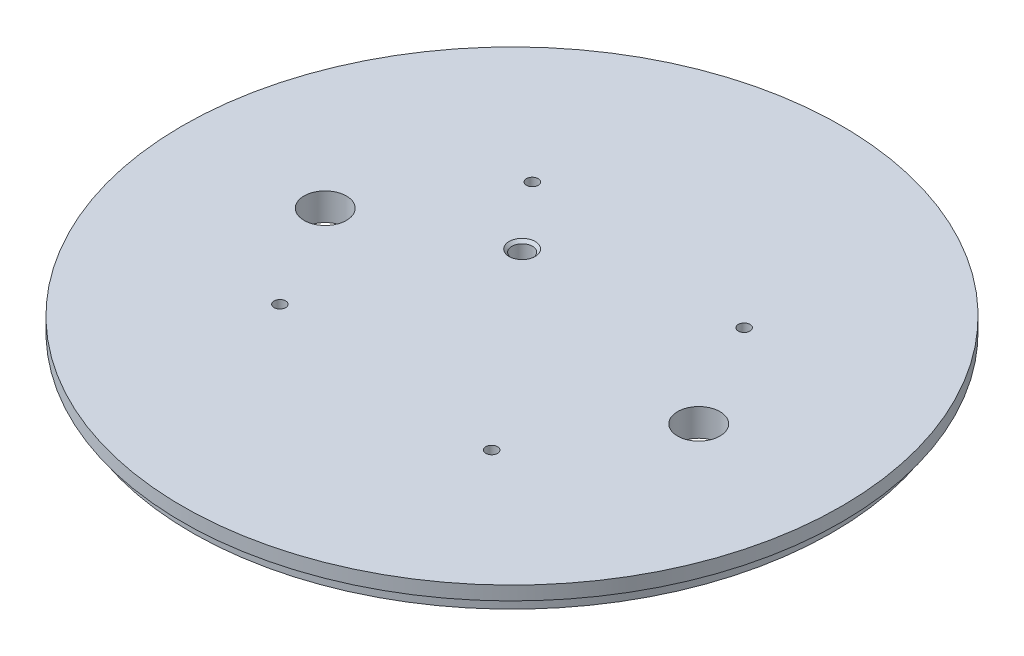
SolidWorks part; units mm, degrees
material "Delrin 2700 NC010, Low Viscosity Acetal Copolymer (SS)"
ref_plane "Front Plane" through (0, 0, 0) normal (0, 0, 1) x (1, 0, 0)
ref_plane "Top Plane" through (0, 0, 0) normal (0, 1, 0) x (1, 0, 0)
ref_plane "Right Plane" through (0, 0, 0) normal (1, 0, 0) x (0, 0, -1)
sketch "Sketch1" plane through (0, 0, 0) normal (0, 1, 0) x (1, 0, 0)
  circle A0 centre (0, 0) radius 76.2
  dimension "D1" = 152.4
extrude "Boss-Extrude1" add sketch "Sketch1" along normal blind 6.35
hole_wizard "Tap Drill for #4-40 Tap1" [suppressed] positions "Sketch3" profile "Sketch4" hole size "#4-40" standard "ANSI Inch"
sketch "Sketch3" plane through (0, 0, 0) normal (0, -1, 0) x (-1, 0, 0)
  point P0 (0, 25.4)
  point P2 (0, 50.4)
  dimension "D1" = 25.4
  dimension "D2" = 25
sketch "Sketch4" plane through (0, 0, -25.4) normal (1, 0, 0) x (0, 0, -1)
  line L0 (0, 0) -> (0, 10.16)
  line L1 (0, 10.16) -> (1.1303, 10.16)
  line L2 (1.1303, 10.16) -> (1.1303, 0)
  line L5 (1.1303, 0) -> (0, 0)
  line L11 (0, -6.35) -> (0, 107.95) construction
  dimension "Thru Hole Dia." = 2.2606
  dimension "Thru Hole Depth" = 10.16
sketch "Sketch2" [suppressed] plane through (0, 0, 0) normal (0, -1, 0) x (1, 0, 0)
  line L0 (0, 0) -> (0, -55.372) construction
  line L1 (-3.429, -27.686) -> (3.429, -27.686)
  line L2 (-5.969, -30.226) -> (-5.969, -45.574)
  line L3 (-3.429, -48.114) -> (3.429, -48.114)
  line L4 (5.969, -30.226) -> (5.969, -45.574)
  arc A0 (3.429, -48.114) -> (5.969, -45.574) centre (3.429, -45.574) ccw
  arc A1 (-5.969, -45.574) -> (-3.429, -48.114) centre (-3.429, -45.574) ccw
  arc A2 (3.429, -27.686) -> (5.969, -30.226) centre (3.429, -30.226) cw
  arc A3 (-3.429, -27.686) -> (-5.969, -30.226) centre (-3.429, -30.226) ccw
  circle A4 centre (0, -25.4) radius 1.1303 construction
  circle A5 centre (0, -50.4) radius 1.1303 construction
  point P10 (5.969, -27.686)
  point P13 (-5.969, -27.686)
  point P17 (0, -27.686)
  dimension "D2" = 2.54
  dimension "D1" = 11.938
  dimension "D3" = 2.286
  dimension "D4" = 2.286
extrude "Cut-Extrude1" [suppressed] cut sketch "Sketch2" against normal through all
hole_wizard "Tap Drill for #6-32 Tap1" positions "Sketch5" profile "Sketch6" hole size "#6-32" standard "ANSI Inch" end condition through all
sketch "Sketch5" plane through (0, 0, 0) normal (0, -1, 0) x (-1, 0, 0)
  line L0 (0, 0) -> (58.3519, 0) construction
  line L2 (0, 0) -> (37.5212, 6.616) construction
  point P0 (37.5212, 6.616)
  dimension "D1" = 10
  dimension "D2" = 38.1
sketch "Sketch6" plane through (-37.5212, 0, -6.616) normal (1, 0, 0) x (0, 0, -1)
  line L0 (0, 0) -> (0, 6.35)
  line L1 (0, 6.35) -> (1.3525, 6.35)
  line L2 (1.3525, 6.35) -> (1.3525, 0)
  line L5 (1.3525, 0) -> (0, 0)
  line L11 (0, -6.35) -> (0, 107.95) construction
  dimension "Thru Hole Dia." = 2.7051
  dimension "Thru Hole Depth" = 6.35
pattern_circular "CirPattern1" count 4 over 360 about axis through (0, 0, 0) along (0, 1, 0) of "Tap Drill for #6-32 Tap1"
hole_wizard "W (0.386) Diameter Hole1" positions "Sketch7" profile "Sketch8" hole size "W" standard "ANSI Inch" end condition through all
sketch "Sketch7" plane through (0, 0, 0) normal (0, -1, 0) x (-1, 0, 0)
  line L2 (0, 0) -> (-33.0778, 27.7556) construction
  line L4 (0, 0) -> (0, 19.4817) construction
  point P0 (-33.0778, 27.7556)
  point P17 (33.0778, -27.7556)
  dimension "D1" = 50
  dimension "D2" = 43.18
  dimension "D3" = 43.18
sketch "Sketch8" plane through (33.0778, 0, -27.7556) normal (1, 0, 0) x (0, 0, -1)
  line L0 (0, 0) -> (0, 6.35)
  line L1 (0, 6.35) -> (4.9022, 6.35)
  line L2 (4.9022, 6.35) -> (4.9022, 0)
  line L5 (4.9022, 0) -> (0, 0)
  line L11 (0, -6.35) -> (0, 107.95) construction
  dimension "Thru Hole Dia." = 9.8044
  dimension "Thru Hole Depth" = 6.35
hole_wizard "3/16 (0.1875) Diameter Hole1" positions "Sketch10" profile "Sketch11" hole size "3/16" standard "ANSI Inch" end condition through all
sketch "Sketch10" plane through (0, 0, 0) normal (0, -1, 0) x (-1, 0, 0)
  line L0 (0, 0) -> (37.5212, 6.616) construction
  point P0 (18.7606, 3.308)
sketch "Sketch11" plane through (-18.7606, 0, -3.308) normal (1, 0, 0) x (0, 0, -1)
  line L0 (0, 0) -> (0, 6.35)
  line L1 (0, 6.35) -> (3.0162, 6.35)
  line L2 (2.3812, 5.715) -> (2.3812, 0.635)
  line L3 (2.3812, 0.635) -> (3.0162, 0)
  line L5 (3.0162, 0) -> (0, 0)
  line L6 (-2.3812, 0.635) -> (-3.0162, 0) construction
  line L7 (3.0162, 6.35) -> (2.3812, 5.715)
  line L8 (-3.0162, 6.35) -> (-2.3812, 5.715) construction
  line L11 (0, -6.35) -> (0, 107.95) construction
  dimension "Thru Hole Dia." = 4.7625
  dimension "Thru Hole Depth" = 6.35
  dimension "Near C'Sink Dia." = 6.0325
  dimension "Near C'Sink Angle" = 90
  dimension "Far C'Sink Dia." = 6.0325
  dimension "Far C'Sink Angle" = 90
sketch "Sketch12" plane through (0, 0, 0) normal (0, -1, 0) x (1, 0, 0)
  line L0 (0, 0) -> (31.6547, 37.7246) construction
  line L10 (19.8869, 28.7385) -> (24.8486, 24.5751)
  line L11 (19.8869, 28.7385) -> (6.4989, 12.7833)
  line L12 (6.4989, 12.7833) -> (11.4606, 8.62)
  line L13 (24.8486, 24.5751) -> (11.4606, 8.62)
  line L17 (0, 0) -> (-53.1972, 0) construction
  line L18 (-33.0778, 27.7556) -> (33.0778, -27.7556) construction
  circle A0 centre (22.3677, 26.6568) radius 3.2385
  circle A1 centre (8.9797, 10.7016) radius 3.2385
  circle A2 centre (33.0778, -27.7556) radius 4.9022 construction
  circle A3 centre (-33.0778, 27.7556) radius 4.9022 construction
  circle A4 centre (33.0778, -27.7556) radius 4.9022
  circle A5 centre (-33.0778, 27.7556) radius 4.9022
  dimension "D1" = 6.477
  dimension "D2" = 13.97
  dimension "D3" = 20.828
extrude "Cut-Extrude4" cut sketch "Sketch12" against normal blind 3.175 contours A1 L13 A0 L11 | L10 A0 | L12 A1 | L12 A1 | L10 A0
ref_plane "Plane1" through (0, 0, 0) normal (0.6428, 0, 0.766) x (0.766, 0, -0.6428)
mirror "Mirror1" about plane through (0, 0, 0) normal (0.6428, 0, 0.766) of "Cut-Extrude4"
sketch "Sketch15" plane through (0, 0, 0) normal (0, -1, 0) x (1, 0, 0)
  circle A0 centre (0, 0) radius 74.041
  circle A1 centre (0, 0) radius 76.2 construction
  circle A2 centre (0, 0) radius 76.2
  dimension "D1" = 148.082
extrude "Cut-Extrude5" cut sketch "Sketch15" against normal blind 3.175
sketch "Sketch17" plane through (0, 6.35, 0) normal (0, 1, 0) x (1, 0, 0)
  circle A0 centre (-33.0778, -27.7556) radius 9.525
  circle A1 centre (33.0778, 27.7556) radius 9.525
  dimension "D1" = 19.05
  dimension "D2" = 19.05
split line "Split Line1" [suppressed]
sketch "Sketch19" plane through (0, 0, 0) normal (0, -1, 0) x (1, 0, 0)
  circle A0 centre (-33.0778, 27.7556) radius 9.525
  circle A1 centre (33.0778, -27.7556) radius 9.525
  dimension "D1" = 19.05
  dimension "D2" = 19.05
split line "Split Line2" [suppressed]
sketch "Sketch18" [suppressed] plane through (0, 6.35, 0) normal (0, 1, 0) x (1, 0, 0)
  circle A0 centre (0, 0) radius 76.2 construction
  circle A1 centre (33.0778, 27.7556) radius 9.525 construction
  circle A2 centre (-33.0778, -27.7556) radius 9.525 construction
  circle A3 centre (0, 0) radius 76.2
  circle A4 centre (33.0778, 27.7556) radius 9.525
  circle A5 centre (-33.0778, -27.7556) radius 9.525
  circle A7 centre (0, 0) radius 12.7
  circle A8 centre (-18.7606, 3.308) radius 9.525
  dimension "D1" = 25.4
  dimension "D2" = 19.05
extrude "Cut-Extrude6" [suppressed] cut sketch "Sketch18" against normal blind 4.7625
sketch "Sketch20" [suppressed] plane through (0, 6.35, 0) normal (0, 1, 0) x (1, 0, 0)
  line L0 (-5.3508, -4.4899) -> (5.3508, 4.4899) construction
  line L1 (5.7551, 2.6836) -> (64.7444, 30.1908)
  line L2 (0, 0) -> (-82.2548, -38.356) construction
  line L3 (0, 0) -> (46.1621, 65.9264) construction
  line L4 (0, 0) -> (-109.7287, 0) construction
  line L5 (3.6422, 5.2016) -> (40.9749, 58.5182)
  line L6 (-64.7444, -30.1908) -> (-5.7551, -2.6836)
  line L7 (-40.9749, -58.5182) -> (-3.6422, -5.2016)
  circle A0 centre (0, 0) radius 71.4375
  circle A1 centre (0, 0) radius 6.35
  circle A2 centre (-62.2864, -23.7898) radius 4.7625
  circle A4 centre (34.2443, 57.2091) radius 4.7625
  circle A7 centre (1.8576, 10.9561) radius 4.7625
  circle A8 centre (-11.1123, 0.0731) radius 4.7625
  circle A9 centre (-1.8576, -10.9561) radius 4.7625
  circle A10 centre (11.1123, -0.0731) radius 4.7625
  circle A11 centre (62.2864, 23.7898) radius 4.7625
  circle A12 centre (-34.2443, -57.2091) radius 4.7625
  dimension "D1" = 142.875
  dimension "D2" = 12.7
  dimension "D4" = 9.525
  dimension "D3" = 25
  dimension "D5" = 150
extrude "Cut-Extrude7" [suppressed] cut sketch "Sketch20" against normal blind 2.54
move or copy body "Body-Move/Copy1" bodies to move or copy 111 copy no rotation origin (0, 0, 0) rotation axis (0, -1, 0) rotation angle 40
chamfer "Chamfer1" [suppressed] distance 0.635 angle 45
equation "\"Bodytube_OD\" = 6.17in"
equation "\"Bodytube_ID\" = 5.998in"
equation "\"Camera_Cutout_Width\"=10mm"
equation "\"Camera_Cutout_Height\"=7mm"
equation "\"Fwd_Tube_Length\" = 38.5in"
equation "\"BKHD_Screw_Diam\"= 3.5mm"
equation "\"Fwd_BKHD_From_Top\" = 18in"
equation "\"Shear_Screw_Diameter\" = 0.086in"
equation "\"Shear_Screw_Coupler_Location\" = 4.5in"
equation "\"Motor_OD\" = 4in"
equation "\"Mid_Coupler_Length\" = 13in"
equation "\"Aft_Section_Length\"= 36in"
equation "\"AB_Coupler_OD_Length\"= 1in"
equation "\"AB_Coupling_Section_Length\"= 0.375in"
equation "\"AB_Coupler_Length\"= \"AB_Coupler_OD_Length\" + \"AB_Coupling_Section_Length\" * 2"
equation "\"Cutout_Angle\" = 80"
equation "\"AB_Paddle_Height\" = 0.375in"
equation "\"AB_Coupler_Num_Screws\"= 4"
equation "\"AB_BKHD_Thickness\" = 0.375in"
equation "\"AB_Mount_From_Bottom\" = 23.175in"
equation "\"Num_Cutouts\" = 3"
equation "\"AB_Coupler_OD\"= 6.17in"
equation "\"AB_Coupler_ID\"= 5.75in"
equation "\"AB_Coupler_Surface_Diameter\"= 5.998in"
equation "\"AB_Coupling_Screw_Diameter\"= 0.15748in"
equation "\"AB_Central_Bushing_Length\" = .4724in"
equation "\"Lead_Screw_Dist\" = 3.4in"
equation "\"Lead_Screw_Diam\" = 0.386in"
equation "\"Lead_Screw_Length\" = (\"Mid_Coupler_Length\" + 2*0.375in + 2*.75in)"
equation "\"Paddle_Pin_Offset\" = .25in"
equation "\"Paddle_Pin_Radius\" = 2.25in"
equation "\"SS_Paddle_Pin_Radius\" = 2.25*0.66in"
equation "\"Paddle_Gear_OD\" = 3.2in"
equation "\"Drive_Gear_OD\" = 1.7in"
equation "\"Fin_Thickness\"= .118in"
equation "\"Guiderail_Cutout_Diameter\"= 1.5in"
equation "\"DB9_Hole_Dist\" = 25mm"
equation "\"DB9_Relief_Width\" = 0.47in"
equation "\"DB9_Relief_Hole_Offset\" = 0.09in"
equation "\"Airbrakes_Wire_Hole_Dia\" = .25in"
equation "\"Airbrakes_Wire_Hole_Dist\" = 1.1in"
equation "\"Servo_Gear_Offset\" = 0.5in"
equation "\"FWD_Shear_Screw_Dist\" = 1.5in"
equation "\"Camera_Screw_Dia\" = 0.216535"
equation "\"Camera_Hole_Angle\" = atn ( 2 / 3 * tan ( 12.5deg ) )"
equation "\"Coupler_OD\" = 5.998"
equation "\"Coupler_ID\" = 5.8"
equation "\"Mounting_Bracket_Centerhole_DIA\" = 0.4in"
equation "\"Drive_Gear_Shaft_DIA\" = \"Mounting_Bracket_Centerhole_DIA\" - 0.02in"
equation "\"Drive_Gear_Fillet\" = 0.22in"
equation "\"Drive_Gear_ID\" = 0.62in"
equation "\"Drive_Gear_Offset\" = 0.01in"
equation "\"D1@Sketch2\"=\"DB9_Relief_Width\""
equation "\"D2@Sketch3\"=\"DB9_Hole_Dist\""
equation "\"D3@Sketch2\"=\"DB9_Relief_Hole_Offset\""
equation "\"D4@Sketch2\"=\"DB9_Relief_Hole_Offset\""
equation "\"D2@Sketch7\"=\"Lead_Screw_Dist\"/2"
equation "\"D3@Sketch7\"=\"Lead_Screw_Dist\"/2"
